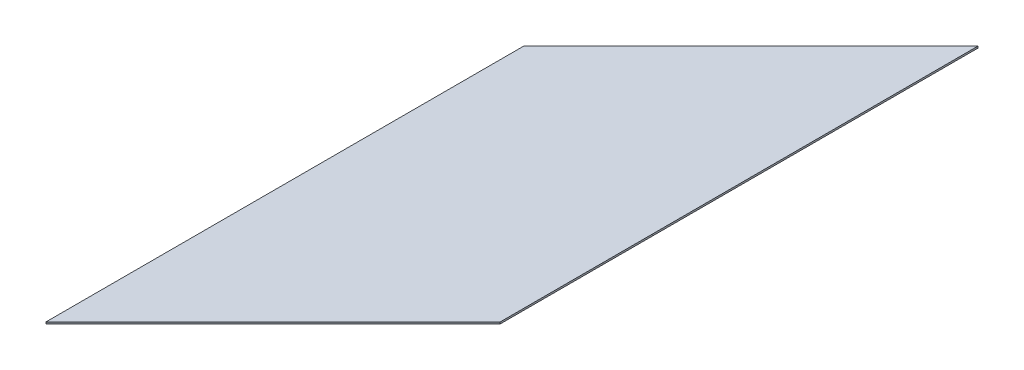
SolidWorks part; units mm, degrees
material "Balsa"
ref_plane "Front Plane" through (0, 0, 0) normal (0, 0, 1) x (1, 0, 0)
ref_plane "Top Plane" through (0, 0, 0) normal (0, 1, 0) x (1, 0, 0)
ref_plane "Right Plane" through (0, 0, 0) normal (1, 0, 0) x (0, 0, -1)
sketch "Sketch1" plane through (0, 0, 0) normal (0, 1, 0) x (1, 0, 0)
  line L0 (322.2005, 538.0575) -> (322.2005, 1000)
  line L1 (322.2005, 1000) -> (0, 677.7995)
  line L2 (0, 677.7995) -> (0, 0)
  line L3 (0, 0) -> (322.2, 322.2)
  line L4 (322.2, 322.2) -> (322.2, 468.2496)
  line L5 (322.2005, 538.0575) -> (322.2, 468.2496)
extrude "Boss-Extrude1" add sketch "Sketch1" along normal blind 2.54
